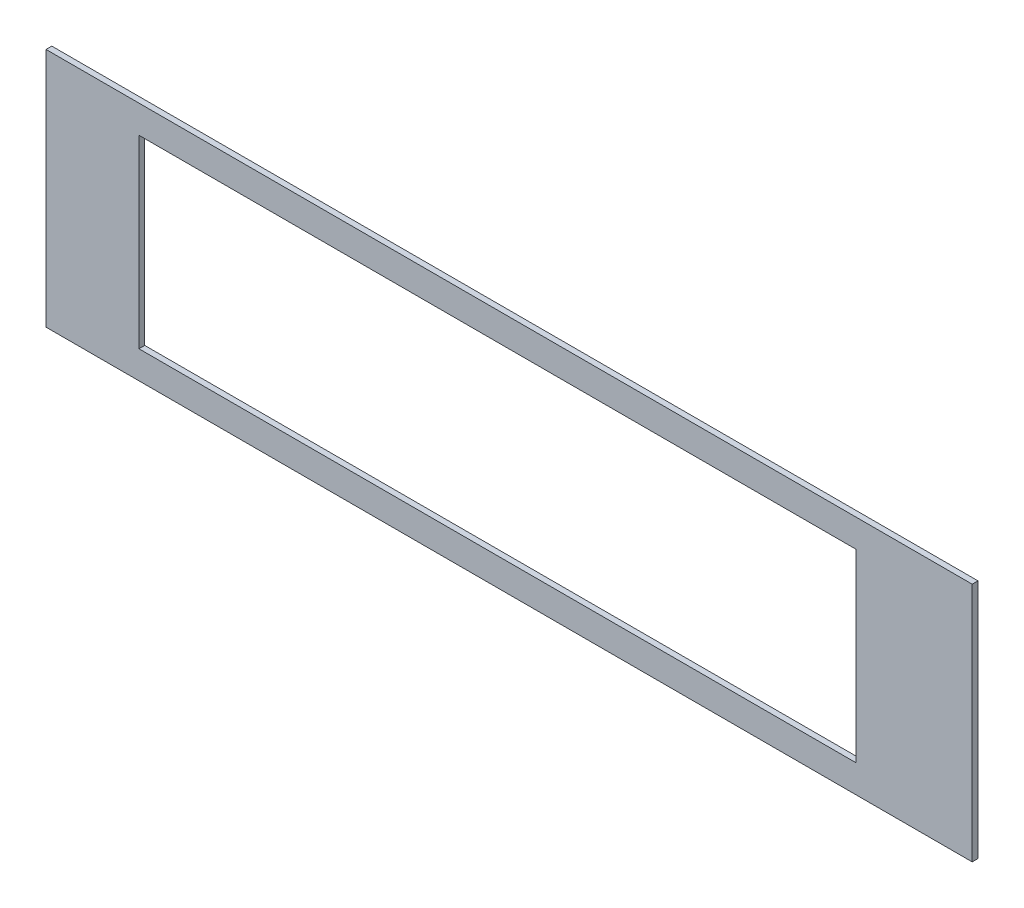
SolidWorks part; units mm, degrees
ref_plane "Front" through (0, 0, 0) normal (0, 0, 1) x (1, 0, 0)
ref_plane "Top" through (0, 0, 0) normal (0, 1, 0) x (1, 0, 0)
ref_plane "Right" through (0, 0, 0) normal (1, 0, 0) x (0, 0, -1)
sketch "Sketch1" plane through (0, 0, 0) normal (0, 0, 1) x (1, 0, 0)
  line L0 (-254.1016, -65.986) -> (254.1016, -65.986)
  line L1 (254.1016, -65.986) -> (254.1016, 65.986)
  line L2 (254.1016, 65.986) -> (-254.1016, 65.986)
  line L3 (-254.1016, 65.986) -> (-254.1016, -65.986)
  line L4 (-203.0984, -50.7492) -> (190.3984, -50.7492)
  line L5 (190.3984, -50.7492) -> (190.3984, 50.6984)
  line L6 (190.3984, 50.6984) -> (-203.0984, 50.6984)
  line L7 (-203.0984, 50.6984) -> (-203.0984, -50.7492)
extrude "Boss-Extrude1" add sketch "Sketch1" along normal blind 3.175
